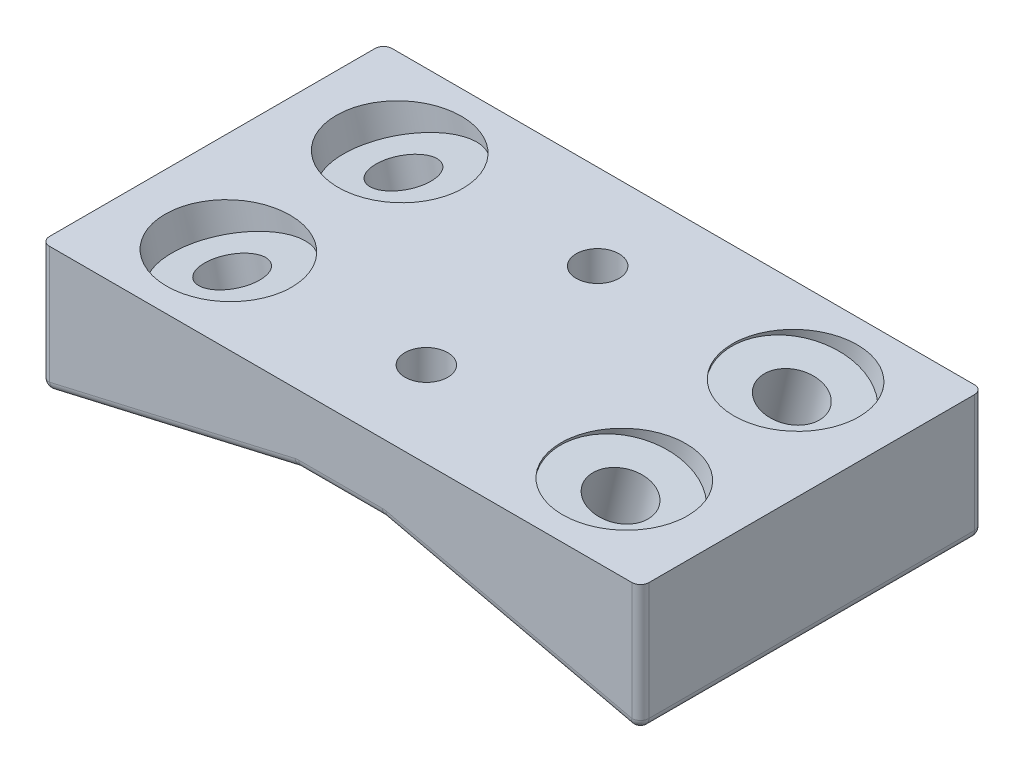
SolidWorks part; units mm, degrees
ref_plane "Front Plane" through (0, 0, 0) normal (0, 0, 1) x (1, 0, 0)
ref_plane "Top Plane" through (0, 0, 0) normal (0, 1, 0) x (1, 0, 0)
ref_plane "Right Plane" through (0, 0, 0) normal (1, 0, 0) x (0, 0, -1)
sketch "Sketch1" plane through (0, 0, 0) normal (0, 0, 1) x (1, 0, 0)
  line L0 (0, 0) -> (0, 15)
  line L1 (0, 15) -> (70, 15)
  line L2 (70, 15) -> (70, 0)
  line L3 (70, 0) -> (40, 6.926)
  line L4 (30, 6.926) -> (0, 0)
  line L5 (30, 6.926) -> (40, 6.926)
  line L6 (35, 6.926) -> (35, 15) construction
  dimension "D1" = 15
  dimension "D2" = 70
  dimension "D3" = 13
  dimension "D4" = 10
extrude "Boss-Extrude1" add sketch "Sketch1" against normal blind 40
hole_wizard "Ø5.0 (5) Diameter Hole1" positions "Sketch3" profile "Sketch2" hole size "Ø5.0" standard "ANSI Metric"
sketch "Sketch3" plane through (0, 15, 0) normal (0, 1, 0) x (1, 0, 0)
  line L0 (35, 0) -> (35, 40) construction
  line L1 (70, 0) -> (0, 0) construction
  line L2 (70, 40) -> (0, 40) construction
  point P9 (35, 10)
  point P11 (35, 30)
  dimension "D1" = 20
  dimension "D2" = 10
sketch "Sketch2" plane through (35, 15, -10) normal (1, 0, 0) x (0, 0, 1)
  line L0 (0, 0) -> (0, 20.5022)
  line L1 (0, 20.5022) -> (2.5, 19)
  line L2 (2.5, 19) -> (2.5, 0)
  line L5 (2.5, 0) -> (0, 0)
  line L10 (0, 20.5022) -> (-2.5, 19) construction
  line L11 (0, -6.35) -> (0, 107.95) construction
  dimension "Hole Dia." = 5
  dimension "Hole Depth" = 19
  dimension "Drill Angle" = 118
ref_plane "Plane1" through (35, 0, 0) normal (1, 0, 0) x (0, 0, -1)
fillet "Fillet1" radius 1 14 edges at (70, 7.5, -40) (55, 3.463, -40) (15, 3.463, -40) (0, 7.5, -40) (0, 0, -20) (0, 7.5, 0) (15, 3.463, 0) (55, 3.463, 0) (70, 0, -20) (70, 7.5, 0) (30, 6.926, -20) (40, 6.926, -20) (35, 6.926, -40) (35, 6.926, 0)
hole_wizard "M6 Clearance Hole3" positions "Sketch13" profile "Sketch12" hole size "M6" standard "ANSI Metric" end condition through all
sketch "Sketch13" plane through (0, 0, 0) normal (0.225, -0.9744, 0) x (-0.9744, -0.225, 0)
  point P0 (-14.9572, 10)
  point P3 (-14.9572, 30)
sketch "Sketch12" plane through (14.5738, 3.3646, -10) normal (0, 0, 1) x (0.9744, 0.225, 0)
  line L0 (0, 0) -> (0, 14.6156)
  line L1 (0, 14.6156) -> (3.3, 14.6156)
  line L2 (3.3, 14.6156) -> (3.3, 0)
  line L5 (3.3, 0) -> (0, 0)
  line L11 (0, -6.35) -> (0, 107.95) construction
  dimension "Thru Hole Dia." = 6.6
  dimension "Thru Hole Depth" = 14.6156
hole_wizard "M6 Clearance Hole4" positions "Sketch15" profile "Sketch14" hole size "M6" standard "ANSI Metric"
sketch "Sketch15" plane through (3.5422, 15.343, 0) normal (-0.225, -0.9744, 0) x (-0.9744, 0.225, 0)
  point P0 (-53.2487, 10)
  point P3 (-53.2487, 30)
sketch "Sketch14" plane through (55.4262, 3.3646, -10) normal (0, 0, 1) x (0.9744, -0.225, 0)
  line L0 (0, 0) -> (0, 20.9828)
  line L1 (0, 20.9828) -> (3.3, 19)
  line L2 (3.3, 19) -> (3.3, 0)
  line L5 (3.3, 0) -> (0, 0)
  line L10 (0, 20.9828) -> (-3.3, 19) construction
  line L11 (0, -6.35) -> (0, 107.95) construction
  dimension "Hole Dia." = 6.6
  dimension "Hole Depth" = 19
  dimension "Drill Angle" = 118
sketch "Sketch16" plane through (0, 0, 0) normal (0.225, -0.9744, 0) x (0.9744, 0.225, 0)
  circle A0 centre (14.9572, -10) radius 7.2
  circle A1 centre (14.9572, -30) radius 7.2
  dimension "D1" = 14.4
extrude "Cut-Extrude2" cut sketch "Sketch16" against normal through all from offset 10 offset against normal yes
sketch "Sketch17" plane through (3.5422, 15.343, 0) normal (-0.225, -0.9744, 0) x (0.9744, -0.225, 0)
  circle A0 centre (53.2487, -10) radius 7.2
  circle A1 centre (53.2487, -30) radius 7.2
  dimension "D1" = 14.4
extrude "Cut-Extrude3" cut sketch "Sketch17" against normal through all from offset 10 offset against normal yes
